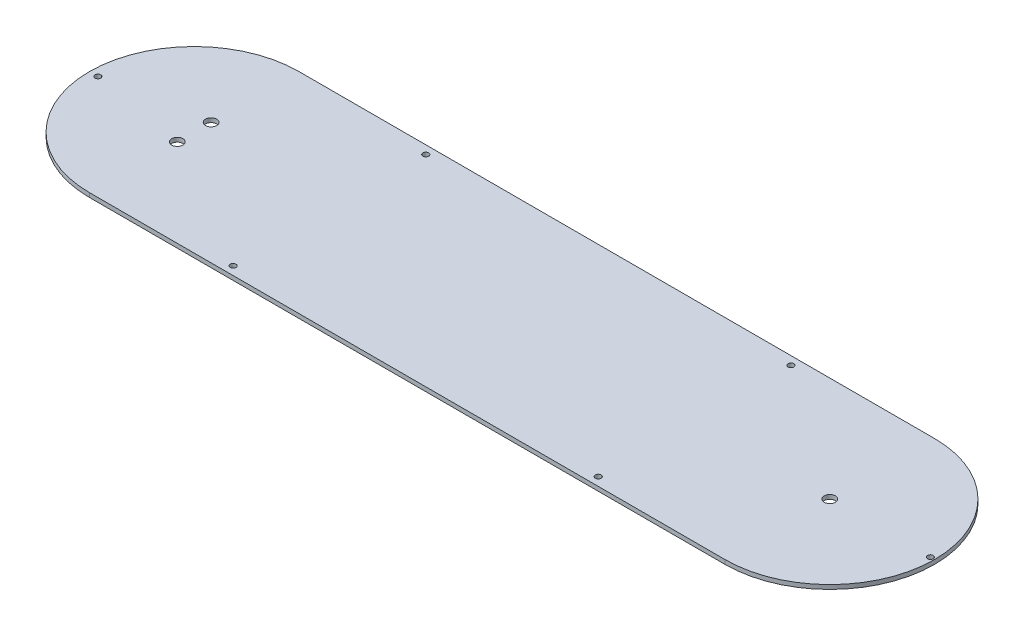
SolidWorks part; units mm, degrees
ref_plane "Front Plane" through (0, 0, 0) normal (0, 0, 1) x (1, 0, 0)
ref_plane "Top Plane" through (0, 0, 0) normal (0, 1, 0) x (1, 0, 0)
ref_plane "Right Plane" through (0, 0, 0) normal (1, 0, 0) x (0, 0, -1)
sketch "Sketch1" plane through (0, 0, 0) normal (0, 1, 0) x (1, 0, 0)
  line L0 (0, 39.37) -> (238.76, 39.37)
  line L1 (0, -39.37) -> (238.76, -39.37)
  line L2 (0, 0) -> (238.76, 0) construction
  arc A0 (0, 39.37) -> (0, -39.37) centre (0, 0) ccw
  arc A1 (238.76, -39.37) -> (238.76, 39.37) centre (238.76, 0) ccw
  circle A2 centre (50.8, 36.195) radius 1.0922
  circle A3 centre (187.96, 36.195) radius 1.0922
  circle A4 centre (50.8, -36.195) radius 1.0922
  circle A5 centre (187.96, -36.195) radius 1.0922
  circle A6 centre (-36.195, 0) radius 1.0922
  circle A7 centre (276.5425, 0) radius 1.0922
  circle A8 centre (238.76, 0) radius 2.1
  circle A9 centre (0, 0) radius 6.35 construction
  circle A10 centre (0, -6.35) radius 2.1
  circle A11 centre (0, 6.35) radius 2.1
  point P27 (0, 0)
  dimension "D1" = 78.74
  dimension "D3" = 4.2
  dimension "D7" = 2.1844
  dimension "D8" = 2.1844
  dimension "D9" = 2.1844
  dimension "D10" = 2.1844
  dimension "D13" = 12.7
  dimension "D14" = 4.2
  dimension "D2" = 238.76
  dimension "D4" = 50.8
  dimension "D5" = 50.8
  dimension "D6" = 3.175
  dimension "D11" = 3.175
  dimension "D12" = 1.5875
  dimension "D15" = 2
extrude "Boss-Extrude1" add sketch "Sketch1" along normal blind 1.5875
